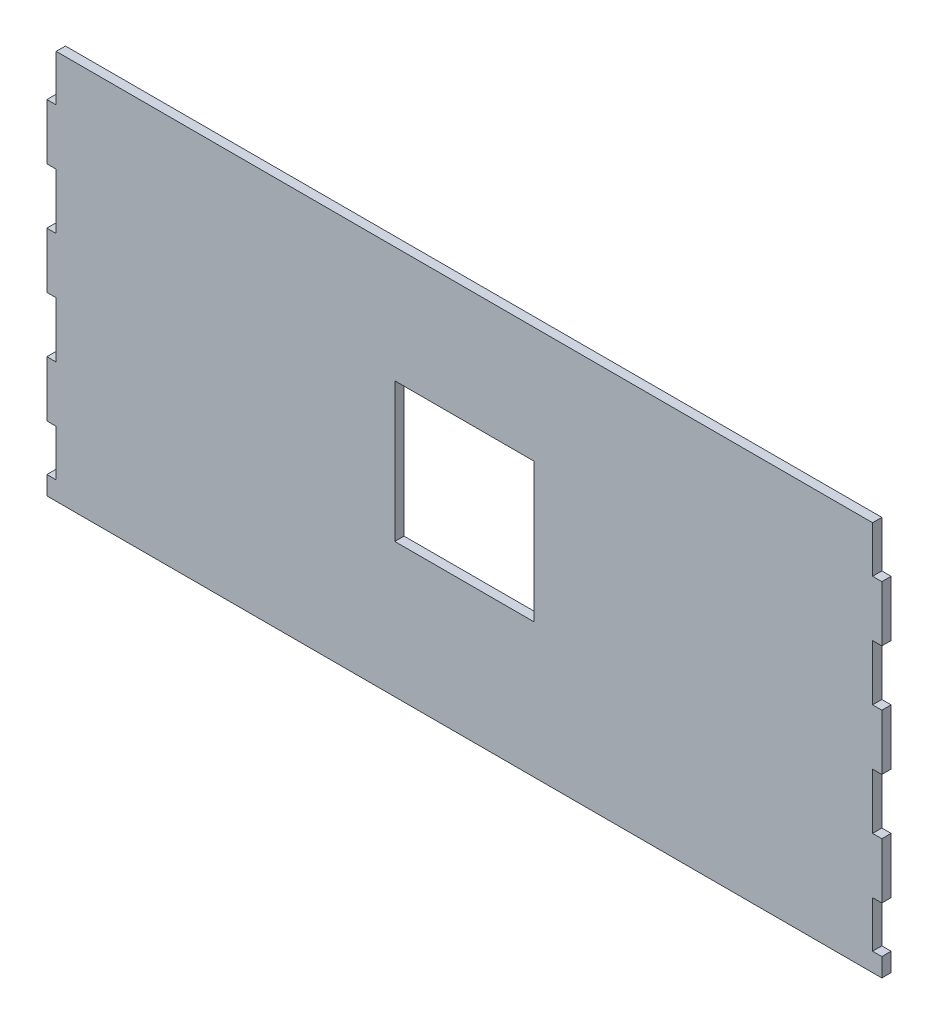
SolidWorks part; units mm, degrees
ref_plane "Front Plane" through (0, 0, 0) normal (0, 0, 1) x (1, 0, 0)
ref_plane "Top Plane" through (0, 0, 0) normal (0, 1, 0) x (1, 0, 0)
ref_plane "Right Plane" through (0, 0, 0) normal (1, 0, 0) x (0, 0, -1)
sketch "Sketch1" plane through (0, 0, 0) normal (0, 0, 1) x (1, 0, 0)
  line L1 (-225, 105) -> (225, 105)
  line L2 (-225, 105) -> (-225, -105)
  line L3 (-225, -105) -> (225, -105)
  line L4 (225, 105) -> (225, -105)
  line L5 (-225, 105) -> (225, -105) construction
  line L6 (-225, -105) -> (225, 105) construction
  point P0 (0, 0)
  dimension "D1" = 450
  dimension "D2" = 210
extrude "Boss-Extrude1" add sketch "Sketch1" along normal blind 5
sketch "Sketch3" plane through (0, 0, 0) normal (0, 0, -1) x (-1, 0, 0)
  line L0 (-225, 105) -> (225, 105) construction
  line L1 (-285.8214, 105) -> (-220, 105)
  line L2 (-285.8214, 105) -> (-285.8214, 80)
  line L3 (-285.8214, 80) -> (-220, 80)
  line L4 (-220, 105) -> (-220, 80)
  line L5 (-285.8214, 105) -> (-220, 80) construction
  line L6 (-285.8214, 80) -> (-220, 105) construction
  line L7 (-363.2287, 50) -> (-220, 50)
  line L8 (-363.2287, 50) -> (-363.2287, 20)
  line L9 (-363.2287, 20) -> (-220, 20)
  line L10 (-220, 50) -> (-220, 20)
  line L11 (-363.2287, 50) -> (-220, 20) construction
  line L12 (-363.2287, 20) -> (-220, 50) construction
  line L13 (-412.2059, -10) -> (-220, -10)
  line L14 (-412.2059, -10) -> (-412.2059, -40)
  line L15 (-412.2059, -40) -> (-220, -40)
  line L16 (-220, -10) -> (-220, -40)
  line L17 (-412.2059, -10) -> (-220, -40) construction
  line L18 (-412.2059, -40) -> (-220, -10) construction
  line L19 (-414.7079, -95) -> (-220, -95)
  line L20 (-414.7079, -95) -> (-414.7079, -70)
  line L21 (-414.7079, -70) -> (-220, -70)
  line L22 (-220, -95) -> (-220, -70)
  line L23 (-414.7079, -95) -> (-220, -70) construction
  line L24 (-414.7079, -70) -> (-220, -95) construction
  line L25 (-225, -105) -> (-225, 105) construction
  line L26 (225, -105) -> (-225, -105) construction
  line L27 (220, 105) -> (290.8214, 105)
  line L28 (220, 105) -> (220, 80)
  line L29 (220, 80) -> (290.8214, 80)
  line L30 (290.8214, 105) -> (290.8214, 80)
  line L31 (220, 105) -> (290.8214, 80) construction
  line L32 (220, 80) -> (290.8214, 105) construction
  line L33 (220, 50) -> (368.2287, 50)
  line L34 (220, 50) -> (220, 20)
  line L35 (220, 20) -> (368.2287, 20)
  line L36 (368.2287, 50) -> (368.2287, 20)
  line L37 (220, 50) -> (368.2287, 20) construction
  line L38 (220, 20) -> (368.2287, 50) construction
  line L39 (220, -10) -> (414.7059, -10)
  line L40 (220, -10) -> (220, -40)
  line L41 (220, -40) -> (414.7059, -40)
  line L42 (414.7059, -10) -> (414.7059, -40)
  line L43 (220, -10) -> (414.7059, -40) construction
  line L44 (220, -40) -> (414.7059, -10) construction
  line L45 (220, -95) -> (419.7079, -95)
  line L46 (220, -95) -> (220, -70)
  line L47 (220, -70) -> (419.7079, -70)
  line L48 (419.7079, -95) -> (419.7079, -70)
  line L49 (220, -95) -> (419.7079, -70) construction
  line L50 (220, -70) -> (419.7079, -95) construction
  line L51 (225, 105) -> (225, -105) construction
  point P0 (-252.9107, 92.5)
  point P5 (-291.6143, 35)
  point P10 (-316.1029, -25)
  point P15 (-317.354, -82.5)
  point P26 (255.4107, 92.5)
  point P31 (294.1143, 35)
  point P36 (317.3529, -25)
  point P41 (319.854, -82.5)
  dimension "D1" = 0
  dimension "D2" = 25
  dimension "D3" = 30
  dimension "D4" = 5
  dimension "D5" = 5
  dimension "D6" = 30
  dimension "D7" = 30
  dimension "D8" = 30
  dimension "D9" = 5
  dimension "D10" = 25
  dimension "D11" = 10
  dimension "D12" = 5
  dimension "D13" = 25
  dimension "D14" = 30
  dimension "D15" = 30
  dimension "D16" = 30
  dimension "D17" = 30
  dimension "D18" = 25
  dimension "D19" = 5
  dimension "D20" = 5
  dimension "D21" = 5
  dimension "D22" = 5
  dimension "D23" = 30
  dimension "D24" = 10
extrude "Cut-Extrude1" cut sketch "Sketch3" against normal through all
sketch "Sketch4" plane through (0, 0, 0) normal (0, 0, -1) x (-1, 0, 0)
  line L0 (225, 80) -> (225, 50) construction
  line L1 (-37.5, 42.5) -> (37.5, 42.5)
  line L2 (-37.5, 42.5) -> (-37.5, -32.5)
  line L3 (-37.5, -32.5) -> (37.5, -32.5)
  line L4 (37.5, 42.5) -> (37.5, -32.5)
  line L5 (-37.5, 42.5) -> (37.5, -32.5) construction
  line L6 (-37.5, -32.5) -> (37.5, 42.5) construction
  line L8 (-220, 105) -> (220, 105) construction
  point P0 (0, 5)
  dimension "D1" = 75
  dimension "D2" = 75
  dimension "D3" = 187.5
  dimension "D4" = 62.5
extrude "Cut-Extrude2" cut sketch "Sketch4" against normal through all
equation "\"10mmm\"=9.5"
